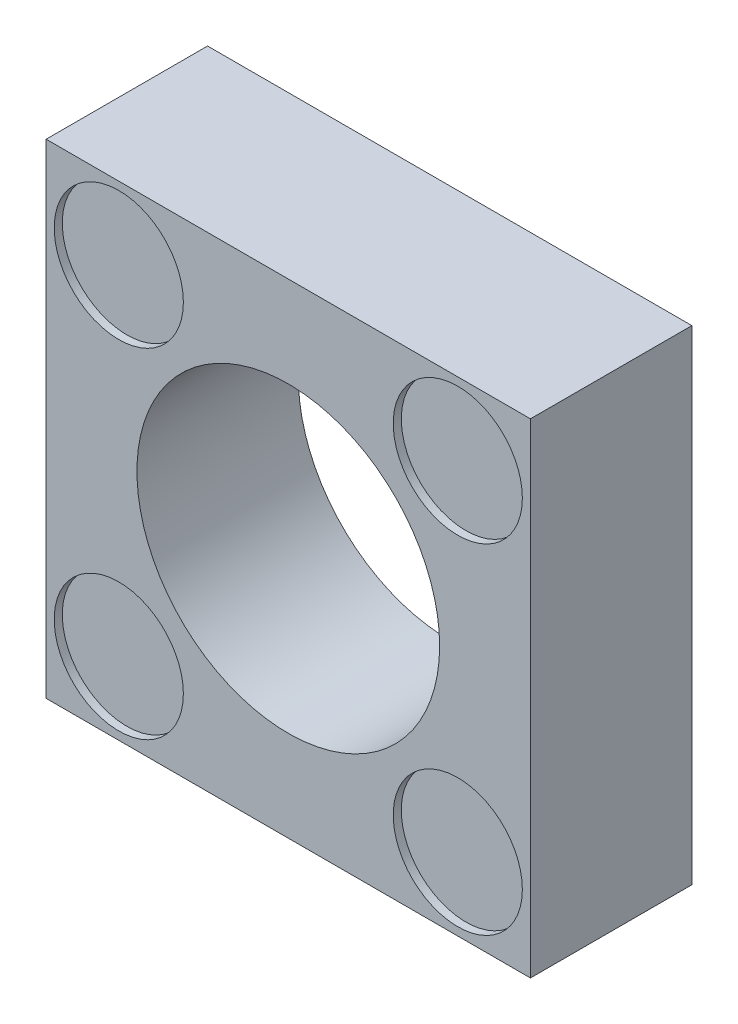
SolidWorks part; units mm, degrees
ref_plane "Alzado" through (0, 0, 0) normal (0, 0, 1) x (1, 0, 0)
ref_plane "Planta" through (0, 0, 0) normal (0, 1, 0) x (1, 0, 0)
ref_plane "Vista lateral" through (0, 0, 0) normal (1, 0, 0) x (0, 0, -1)
sketch "Croquis1" plane through (0, 0, 0) normal (0, 0, 1) x (1, 0, 0)
  line L1 (-300, 300) -> (300, 300)
  line L2 (-300, 300) -> (-300, -300)
  line L3 (-300, -300) -> (300, -300)
  line L4 (300, 300) -> (300, -300)
  line L5 (-300, 300) -> (300, -300) construction
  line L6 (-300, -300) -> (300, 300) construction
  circle A0 centre (0, 0) radius 187.5
  point P0 (0, 0)
  dimension "D3" = 375
  dimension "D1" = 600
  dimension "D2" = 600
extrude "Saliente-Extruir1" add sketch "Croquis1" along normal blind 200
sketch "Croquis2" plane through (0, 0, 200) normal (0, 0, 1) x (1, 0, 0)
  line L0 (-300, 300) -> (-300, -300) construction
  line L1 (300, 300) -> (-300, 300) construction
  line L2 (300, -300) -> (300, 300) construction
  line L3 (-300, -300) -> (300, -300) construction
  circle A0 centre (-210, 210) radius 80
  circle A1 centre (210, 210) radius 80
  circle A2 centre (210, -210) radius 80
  circle A3 centre (-210, -210) radius 80
  dimension "D1" = 160
  dimension "D2" = 160
  dimension "D3" = 160
  dimension "D4" = 160
  dimension "D5" = 90
  dimension "D6" = 90
  dimension "D7" = 90
  dimension "D8" = 90
  dimension "D9" = 90
  dimension "D10" = 90
  dimension "D11" = 90
  dimension "D12" = 90
extrude "Cortar-Extruir1" cut sketch "Croquis2" against normal blind 10
